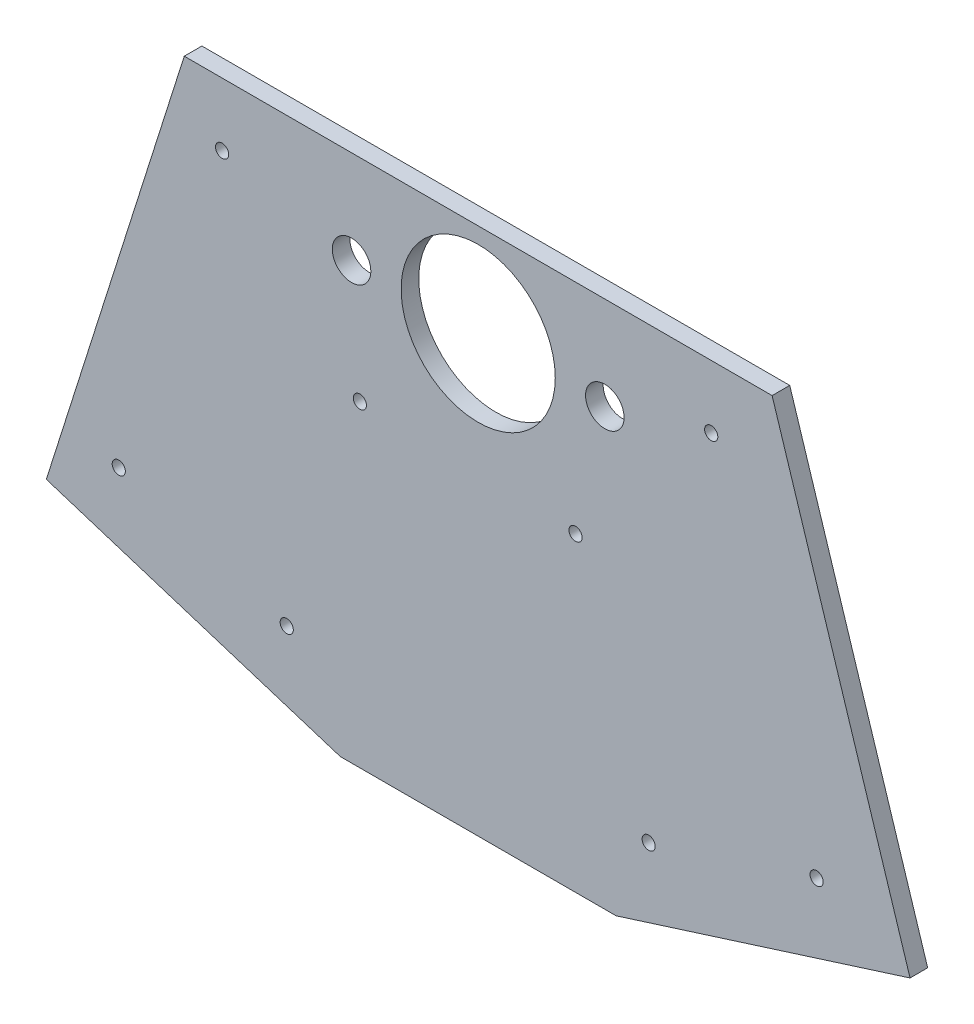
SolidWorks part; units mm, degrees
ref_plane "Front Plane" through (0, 0, 0) normal (0, 0, 1) x (1, 0, 0)
ref_plane "Top Plane" through (0, 0, 0) normal (0, 1, 0) x (1, 0, 0)
ref_plane "Right Plane" through (0, 0, 0) normal (1, 0, 0) x (0, 0, -1)
sketch "Sketch1" plane through (0, 0, 0) normal (0, 0, 1) x (1, 0, 0)
  line L0 (-84.7491, 26.8478) -> (0, 0) construction
  line L1 (0, 0) -> (84.7491, 26.8478) construction
  line L2 (-42.3745, 13.4239) -> (-410.5729, -1148.8491) construction
  line L3 (-410.5729, -1148.8491) -> (-457.2, -1148.8491) construction
  line L4 (-84.7491, 26.8478) -> (84.7491, 26.8478)
  line L5 (84.7491, 26.8478) -> (124.523, -98.7044)
  line L6 (124.523, -98.7044) -> (39.7739, -125.5522)
  line L7 (39.7739, -125.5522) -> (-39.7739, -125.5522)
  line L8 (-39.7739, -125.5522) -> (-124.523, -98.7044)
  line L9 (-124.523, -98.7044) -> (-84.7491, 26.8478)
  line L10 (-39.7739, -125.5522) -> (0, 0) construction
  dimension "D2" = 88.9
  dimension "D3" = 457.2
  dimension "D4" = 1219.2
  dimension "D5" = 152.4
extrude "Boss-Extrude1" add sketch "Sketch1" along normal blind 5.08
sketch "Sketch2" plane through (0, 0, 5.08) normal (0, 0, 1) x (1, 0, 0)
  line L0 (-36.5125, 0) -> (36.5125, 0) construction
  circle A0 centre (0, 0) radius 22.225
  circle A1 centre (-36.5125, 0) radius 5.5562
  circle A2 centre (36.5125, 0) radius 5.5562
  dimension "D1" = 44.45
  dimension "D3" = 11.1125
  dimension "D2" = 73.025
extrude "Cut-Extrude1" cut sketch "Sketch2" against normal through all
hole_wizard "#6 Clearance Hole1" positions "Sketch3" profile "Sketch4" hole size "#6" standard "ANSI Inch" end condition through all
sketch "Sketch3" plane through (0, 0, 5.08) normal (0, 0, 1) x (1, 0, 0)
  line L0 (-109.3892, -103.4987) -> (-68.0965, 26.8478) construction
  line L1 (-124.523, -98.7044) -> (-39.7739, -125.5522) construction
  line L2 (84.7491, 26.8478) -> (-84.7491, 26.8478) construction
  line L3 (-68.0965, 26.8478) -> (-14.8084, 26.8478) construction
  line L4 (-14.8084, 26.8478) -> (-60.9612, -118.8403) construction
  line L6 (-84.7491, 26.8478) -> (-124.523, -98.7044) construction
  line L7 (-103.6361, -85.3381) -> (-55.2081, -100.6797) construction
  line L8 (61.4355, 26.8478) -> (103.3357, -105.4164) construction
  line L9 (39.7739, -125.5522) -> (124.523, -98.7044) construction
  line L12 (8.1474, 26.8478) -> (54.9076, -120.758) construction
  line L14 (49.1545, -102.5974) -> (97.5826, -87.2558) construction
  line L16 (124.523, -98.7044) -> (84.7491, 26.8478) construction
  point P0 (-73.8496, 8.6873)
  point P2 (-103.6361, -85.3381)
  point P4 (-55.2081, -100.6797)
  point P29 (-34.1134, -34.0912)
  point P42 (49.1545, -102.5974)
  point P43 (97.5826, -87.2558)
  point P49 (28.0599, -36.0089)
  point P56 (67.1886, 8.6873)
  dimension "D1" = 15.875
  dimension "D2" = 22.225
  dimension "D3" = 19.05
  dimension "D4" = 19.05
  dimension "D5" = 88.9
  dimension "D6" = 19.05
  dimension "D7" = 22.225
  dimension "D8" = 15.875
  dimension "D9" = 88.9
  dimension "D10" = 19.05
sketch "Sketch4" plane through (-73.8496, 8.6873, 5.08) normal (1, 0, 0) x (0, -1, 0)
  line L0 (0, 0) -> (0, 5.08)
  line L1 (0, 5.08) -> (1.8986, 5.08)
  line L2 (1.8986, 5.08) -> (1.8986, 0)
  line L5 (1.8986, 0) -> (0, 0)
  line L11 (0, -6.35) -> (0, 107.95) construction
  dimension "Thru Hole Dia." = 3.7973
  dimension "Thru Hole Depth" = 5.08
